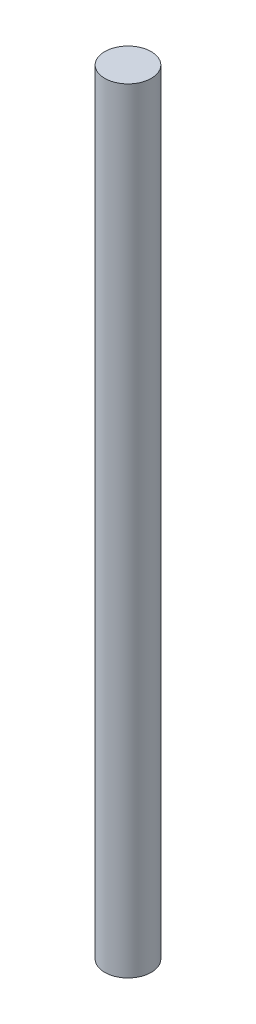
SolidWorks part; units mm, degrees
ref_plane "Front Plane" through (0, 0, 0) normal (0, 0, 1) x (1, 0, 0)
ref_plane "Top Plane" through (0, 0, 0) normal (0, 1, 0) x (1, 0, 0)
ref_plane "Right Plane" through (0, 0, 0) normal (1, 0, 0) x (0, 0, -1)
sketch "Sketch1" plane through (0, 0, 0) normal (0, 1, 0) x (1, 0, 0)
  circle A0 centre (0, 0) radius 30
  dimension "D1" = 60
extrude "Boss-Extrude1" add sketch "Sketch1" along normal blind 1000
